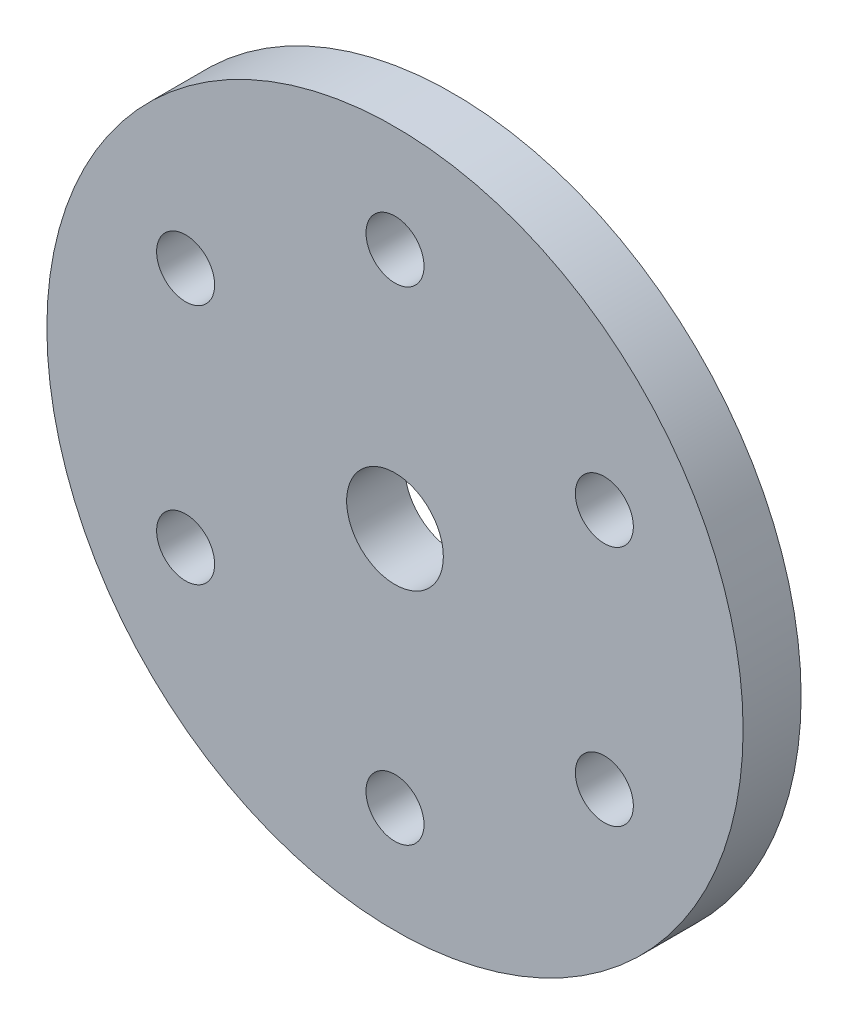
SolidWorks part; units mm, degrees
ref_plane "Front Plane" through (0, 0, 0) normal (0, 0, 1) x (1, 0, 0)
ref_plane "Top Plane" through (0, 0, 0) normal (0, 1, 0) x (1, 0, 0)
ref_plane "Right Plane" through (0, 0, 0) normal (1, 0, 0) x (0, 0, -1)
sketch "Sketch1" plane through (0, 0, 0) normal (0, 0, 1) x (1, 0, 0)
  circle A0 centre (0, 0) radius 18
  circle A1 centre (0, 12.5) radius 1.5
  circle A2 centre (10.8253, 6.25) radius 1.5
  circle A3 centre (10.8253, -6.25) radius 1.5
  circle A4 centre (0, -12.5) radius 1.5
  circle A5 centre (-10.8253, -6.25) radius 1.5
  circle A6 centre (-10.8253, 6.25) radius 1.5
  circle A7 centre (0, 0) radius 2.5
  dimension "D1" = 36
  dimension "D2" = 3
  dimension "D5" = 5
  dimension "D3" = 12.5
  dimension "D4" = 6
extrude "Boss-Extrude1" add sketch "Sketch1" along normal blind 3
